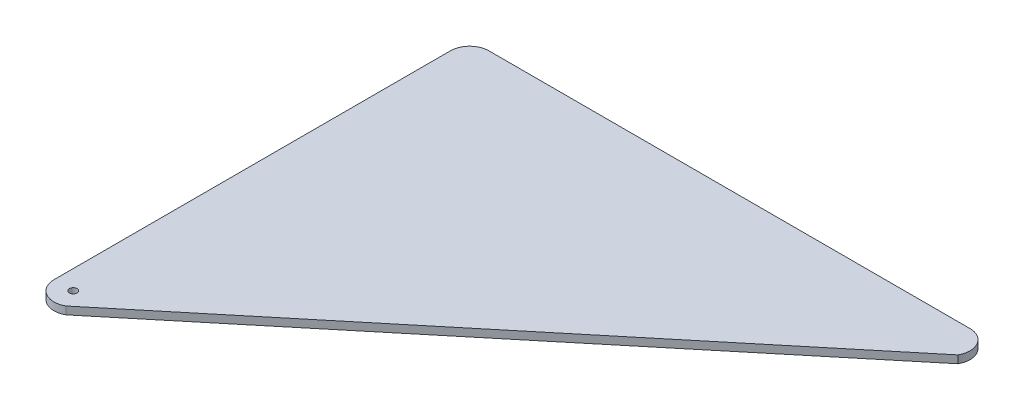
SolidWorks part; units mm, degrees
ref_plane "Plan de face" through (0, 0, 0) normal (0, 0, 1) x (1, 0, 0)
ref_plane "Plan de dessus" through (0, 0, 0) normal (0, 1, 0) x (1, 0, 0)
ref_plane "Plan de droite" through (0, 0, 0) normal (1, 0, 0) x (0, 0, -1)
sketch "Esquisse1" plane through (0, 0, 0) normal (0, 1, 0) x (1, 0, 0)
  line L0 (0, 0) -> (0, 103) construction
  line L3 (129.3338, 100.5) -> (2.5, -4.3301)
  line L4 (-5, 103) -> (-5, 0)
  line L5 (0, 108) -> (125.0037, 108)
  circle A0 centre (0, 0) radius 1
  arc A1 (2.5, -4.3301) -> (-5, 0) centre (0, 0) cw
  arc A3 (125.0037, 108) -> (129.3338, 100.5) centre (125.0037, 103) cw
  arc A4 (-5, 103) -> (0, 108) centre (0, 103) cw
  point P11 (129.3338, 105.5)
  dimension "D2" = 2
  dimension "D3" = 5
  dimension "D4" = 5
  dimension "D1" = 103
  dimension "D5" = 103
  dimension "D6" = 120
  dimension "D7" = 120
  dimension "D8" = 5
extrude "Boss.-Extru.2" add sketch "Esquisse1" along normal blind 2
